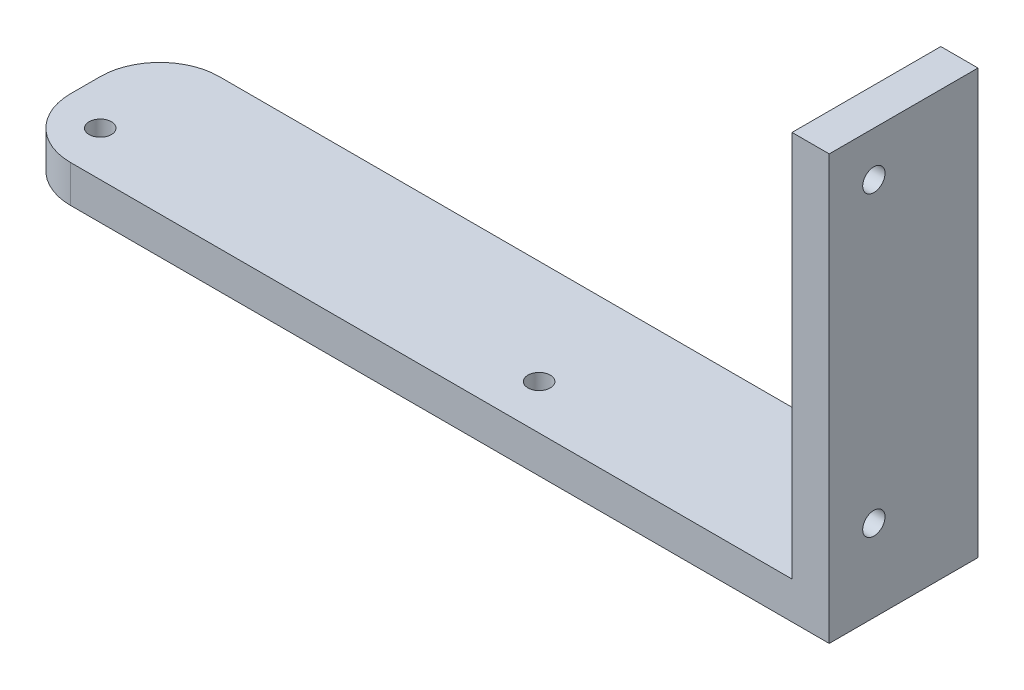
SolidWorks part; units mm, degrees
ref_plane "Front Plane" through (0, 0, 0) normal (0, 0, 1) x (1, 0, 0)
ref_plane "Top Plane" through (0, 0, 0) normal (0, 1, 0) x (1, 0, 0)
ref_plane "Right Plane" through (0, 0, 0) normal (1, 0, 0) x (0, 0, -1)
sketch "Sketch1" plane through (0, 0, 0) normal (0, 1, 0) x (1, 0, 0)
  line L1 (0, 0) -> (110, 0)
  line L2 (0, 0) -> (0, 20)
  line L3 (0, 20) -> (110, 20)
  line L4 (110, 0) -> (110, 20)
  dimension "D1" = 110
  dimension "D2" = 20
extrude "Boss-Extrude1" add sketch "Sketch1" along normal blind 5
sketch "Sketch2" plane through (0, 5, 0) normal (0, 1, 0) x (1, 0, 0)
  line L0 (110, 20) -> (0, 20) construction
  line L1 (110, 0) -> (105, 0)
  line L2 (110, 0) -> (110, 20)
  line L3 (110, 20) -> (105, 20)
  line L4 (105, 0) -> (105, 20)
  dimension "D1" = 5
extrude "Boss-Extrude2" add sketch "Sketch2" along normal blind 52
sketch "Sketch3" plane through (0, 5, 0) normal (0, 1, 0) x (1, 0, 0)
  line L0 (0, 20) -> (0, 0) construction
  line L1 (0, 0) -> (105, 0) construction
  circle A0 centre (6, 6) radius 1.5
  circle A1 centre (65, 6) radius 1.5
  dimension "D1" = 3
  dimension "D2" = 6
  dimension "D3" = 6
  dimension "D4" = 59
extrude "Cut-Extrude1" cut sketch "Sketch3" against normal through all
fillet "Fillet1" radius 8 2 edges at (0, 2.5, 0) (0, 2.5, -20)
sketch "Sketch4" plane through (105, 0, 0) normal (-1, 0, 0) x (0, 0, 1)
  line L1 (-20, 5) -> (0, 5) construction
  line L3 (0, 57) -> (0, 5) construction
  circle A0 centre (-6, 11) radius 1.5
  circle A2 centre (-6, 51) radius 1.5
  dimension "D1" = 6
  dimension "D2" = 3
  dimension "D3" = 6
  dimension "D4" = 40
extrude "Cut-Extrude2" cut sketch "Sketch4" against normal through all
